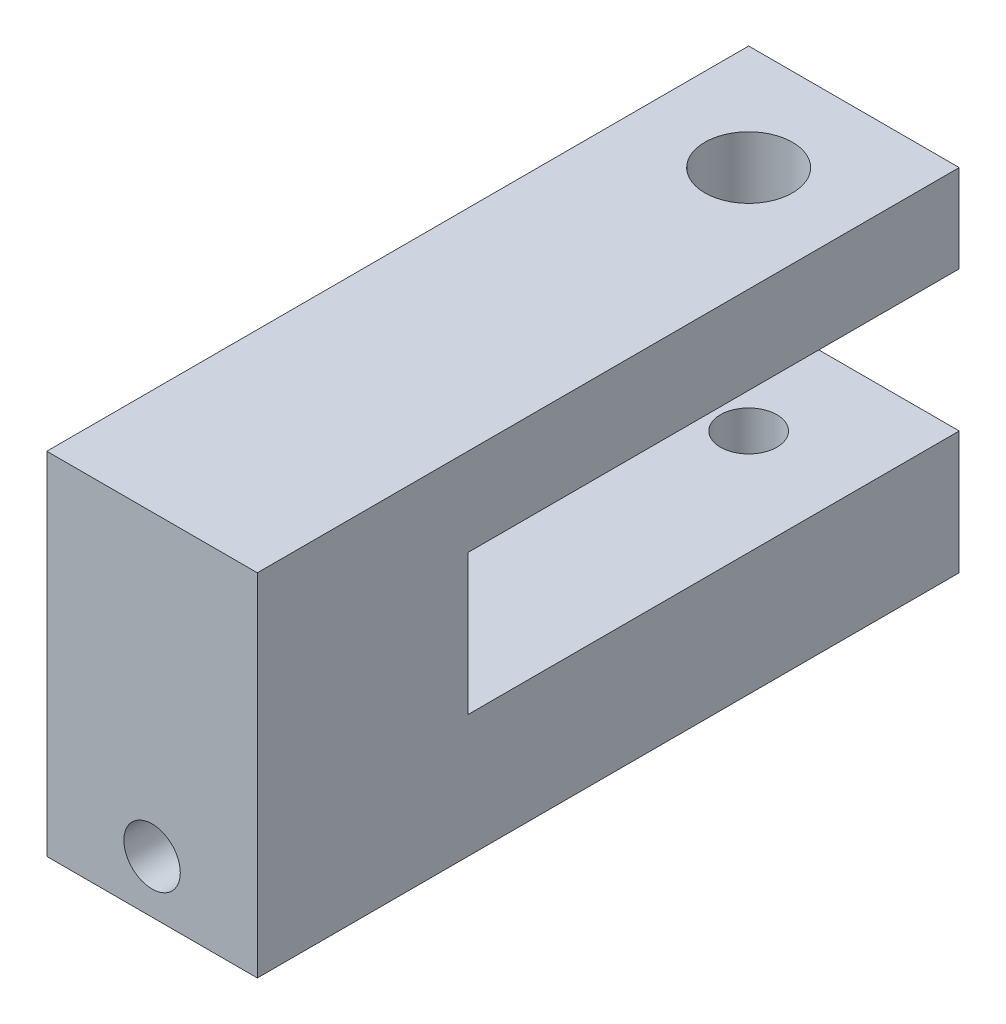
SolidWorks part; units mm, degrees
ref_plane "Front" through (0, 0, 0) normal (0, 0, 1) x (1, 0, 0)
ref_plane "Top" through (0, 0, 0) normal (0, 1, 0) x (1, 0, 0)
ref_plane "Right" through (0, 0, 0) normal (1, 0, 0) x (0, 0, -1)
sketch "Sketch3" plane through (0, 0, 0) normal (1, 0, 0) x (0, 0, -1)
  line L0 (-53.975, 14.2875) -> (-53.975, -17.4625)
  line L1 (-53.975, -17.4625) -> (9.525, -17.4625)
  line L2 (9.525, -17.4625) -> (9.525, -6.35)
  line L3 (9.525, -6.35) -> (-34.925, -6.35)
  line L4 (-34.925, -6.35) -> (-34.925, 6.35)
  line L5 (-34.925, 6.35) -> (9.525, 6.35)
  line L6 (9.525, 6.35) -> (9.525, 14.2875)
  line L7 (9.525, 14.2875) -> (-53.975, 14.2875)
  point P10 (-34.925, 0)
  dimension "D1" = 12.7
  dimension "D2" = 11.1125
  dimension "D3" = 31.75
  dimension "D4" = 19.05
  dimension "D5" = 44.45
  dimension "D6" = 9.525
extrude "Boss-Extrude1" add sketch "Sketch3" along normal mid plane 19.05
hole_wizard "1/4-20 Tapped Hole1" positions "Sketch4" profile "Sketch5" tap size "1/4-20" standard "ANSI Inch" end condition through all
sketch "Sketch4" plane through (0, 14.2875, 0) normal (0, 1, 0) x (1, 0, 0)
  point P0 (0, 0)
sketch "Sketch5" plane through (0, 14.2875, 0) normal (1, 0, 0) x (0, 0, 1)
  line L0 (0, 0) -> (0, 31.75)
  line L1 (0, 31.75) -> (2.5527, 31.75)
  line L2 (2.5527, 31.75) -> (2.5527, 0)
  line L5 (2.5527, 0) -> (0, 0)
  line L11 (0, -6.35) -> (0, 107.95) construction
  dimension "Thru Tap Drill Dia." = 5.1054
  dimension "Thru Tap Drill Depth" = 31.75
cosmetic thread "Hole Thread1" parameters "D2"=6.35
hole_wizard "5/16 (0.3125) Diameter Hole1" positions "Sketch6" profile "Sketch7" hole size "5/16" standard "ANSI Inch"
sketch "Sketch6" plane through (0, 14.2875, 0) normal (0, 1, 0) x (1, 0, 0)
  point P0 (0, 0)
sketch "Sketch7" plane through (0, 14.2875, 0) normal (1, 0, 0) x (0, 0, 1)
  line L0 (0, 0) -> (0, 23.0212)
  line L1 (0, 23.0212) -> (3.9687, 20.6365)
  line L2 (3.9687, 20.6365) -> (3.9687, 0)
  line L5 (3.9687, 0) -> (0, 0)
  line L10 (0, 23.0212) -> (-3.9688, 20.6365) construction
  line L11 (0, -6.35) -> (0, 107.95) construction
  dimension "Hole Dia." = 7.9375
  dimension "Hole Depth" = 20.6365
  dimension "Drill Angle" = 118
hole_wizard "1/4-20 Tapped Hole2" positions "Sketch8" profile "Sketch10" tap size "1/4-20" standard "ANSI Inch"
sketch "Sketch8" plane through (0, 0, 53.975) normal (0, 0, 1) x (1, 0, 0)
  line L0 (9.525, -17.4625) -> (-9.525, -17.4625) construction
  point P0 (0, -12.7)
  point P3 (0, 0)
  point P6 (0, 0)
  dimension "D1" = 4.7625
sketch "Sketch10" plane through (0, -12.7, 53.975) normal (1, 0, 0) x (0, -1, 0)
  line L0 (0, 0) -> (0, 18.0438)
  line L1 (0, 18.0438) -> (2.5527, 16.51)
  line L2 (2.5527, 16.51) -> (2.5527, 0)
  line L5 (2.5527, 0) -> (0, 0)
  line L10 (0, 18.0438) -> (-2.5527, 16.51) construction
  line L11 (0, -6.35) -> (0, 107.95) construction
  dimension "Tap Drill Dia." = 5.1054
  dimension "Tap Drill Depth" = 16.51
  dimension "Drill Angle" = 118
cosmetic thread "Hole Thread2" parameters "D1"=12.7, "D2"=6.35
